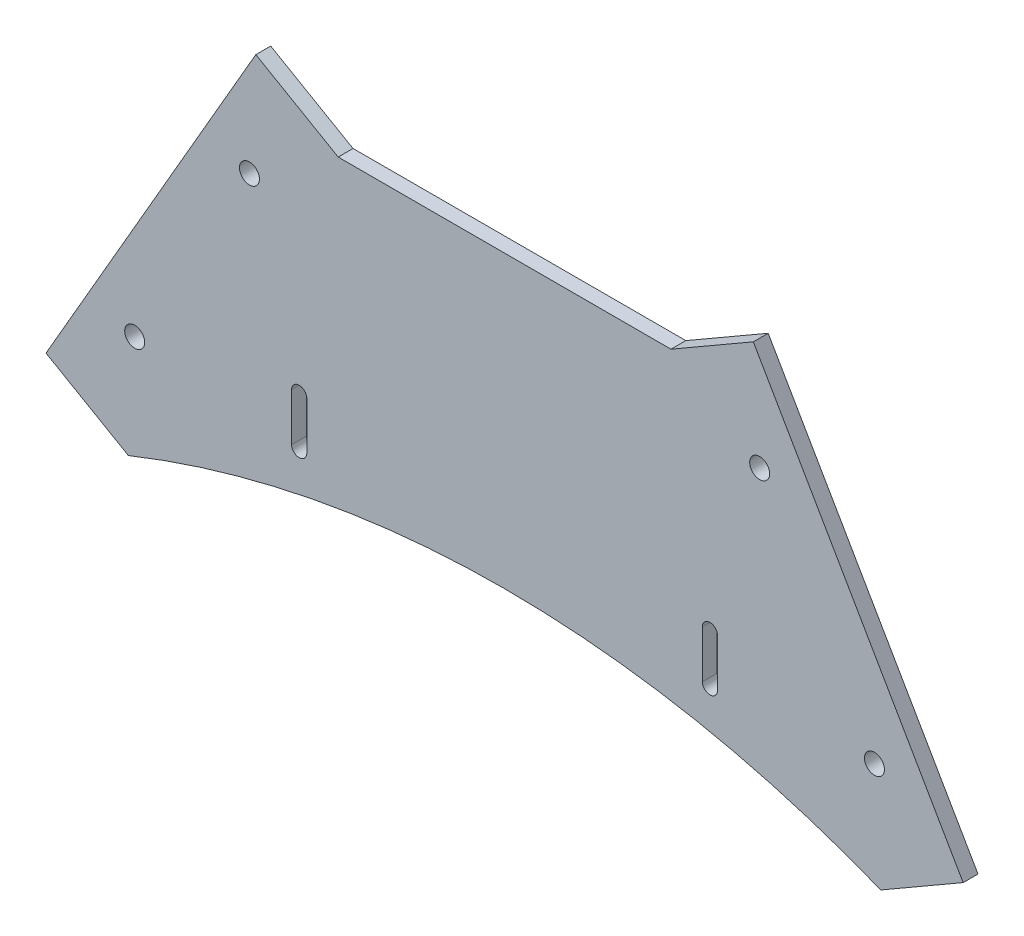
SolidWorks part; units mm, degrees
ref_plane "Front Plane" through (0, 0, 0) normal (0, 0, 1) x (1, 0, 0)
ref_plane "Top Plane" through (0, 0, 0) normal (0, 1, 0) x (1, 0, 0)
ref_plane "Right Plane" through (0, 0, 0) normal (1, 0, 0) x (0, 0, -1)
sketch "Model" plane through (0, 0, 0) normal (0, 0, 1) x (1, 0, 0)
  line L0 (175.591, 0) -> (192.9115, 10)
  line L1 (17.3205, 0) -> (0, 10)
  line L2 (54.8558, 29.1748) -> (54.8558, 19.1748)
  line L3 (141.2558, 29.1748) -> (141.2558, 19.1748)
  line L4 (51.6558, 29.1748) -> (51.6558, 19.1748)
  line L5 (138.0558, 29.1748) -> (138.0558, 19.1748)
  line L9 (61.4558, 76.4445) -> (131.4558, 76.4445)
  line L10 (148.7763, 86.4445) -> (192.9115, 10)
  line L11 (131.4558, 76.4445) -> (148.7763, 86.4445)
  line L12 (44.1352, 86.4445) -> (0, 10)
  line L13 (61.4558, 76.4445) -> (44.1352, 86.4445)
  arc A0 (54.8558, 29.1748) -> (51.6558, 29.1748) centre (53.2558, 29.1748) ccw
  arc A1 (51.6558, 19.1748) -> (54.8558, 19.1748) centre (53.2558, 19.1748) ccw
  arc A2 (138.0558, 19.1748) -> (141.2558, 19.1748) centre (139.6558, 19.1748) ccw
  arc A3 (141.2558, 29.1748) -> (138.0558, 29.1748) centre (139.6558, 29.1748) ccw
  circle A4 centre (42.7955, 64.124) radius 2.1
  circle A5 centre (18.6603, 22.3205) radius 2.1
  circle A6 centre (150.116, 64.124) radius 2.1
  circle A7 centre (174.2512, 22.3205) radius 2.1
  arc A8 (175.591, 0) -> (17.3205, 0) centre (96.4558, -196.7996) ccw
  dimension "D4" = 4.2
  dimension "D5" = 212.1143
  dimension "D12" = 1.6
  dimension "D1" = 20
  dimension "D2" = 88.2705
  dimension "D3" = 70
  dimension "D6" = 86.4
  dimension "D7" = 10
  dimension "D8" = 10
  dimension "D9" = 10
  dimension "D10" = 10
  dimension "D11" = 10
  dimension "D13" = 47.2696
  dimension "D14" = 48.2705
  dimension "D15" = 20
  dimension "D16" = 10
  dimension "D17" = 17.3205
  dimension "D18" = 35.9352
extrude "Boss-Extrude1" add sketch "Model" along normal blind 3.125
